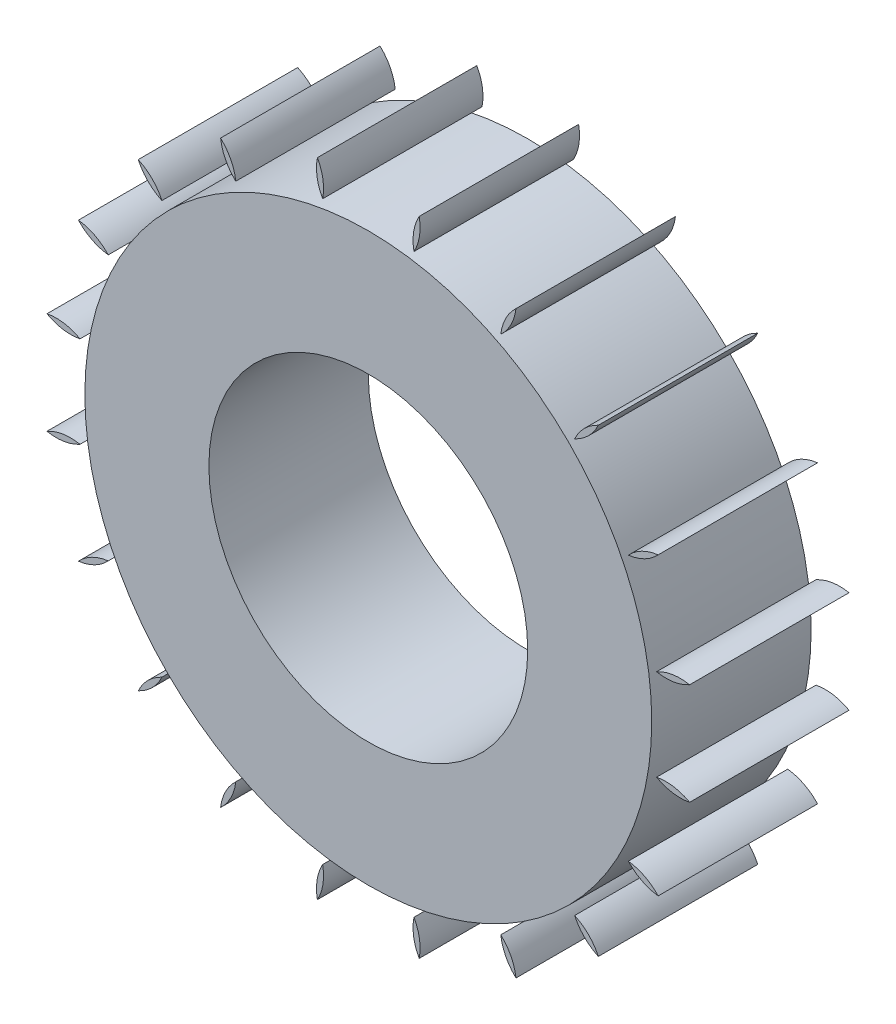
SolidWorks part; units mm, degrees
ref_plane "Front Plane" through (0, 0, 0) normal (0, 0, 1) x (1, 0, 0)
ref_plane "Top Plane" through (0, 0, 0) normal (0, 1, 0) x (1, 0, 0)
ref_plane "Right Plane" through (0, 0, 0) normal (1, 0, 0) x (0, 0, -1)
sketch "Sketch1" plane through (0, 0, 0) normal (0, 0, 1) x (1, 0, 0)
  circle A0 centre (0, 0) radius 6
  circle A1 centre (0, 0) radius 13.2
extrude "Boss-Extrude1" add sketch "Sketch1" along normal blind 6
sketch "Sketch2" plane through (0, 0, 6) normal (0, 0, 1) x (1, 0, 0)
  line L0 (0, 0) -> (0, 15.2) construction
  line L1 (-1.8199, 15.2) -> (0, 0) construction
  line L2 (1.8199, 15.2) -> (0, 0) construction
  arc A0 (-1.8199, 12) -> (1.8199, 12) centre (0, 0) cw
  arc A1 (-2.8199, 12.8953) -> (2.8199, 12.8953) centre (0, 0) cw
  arc A2 (-1.8199, 10.512) -> (1.8199, 10.512) centre (0, 0) cw
  arc A3 (-2.8199, 12.8953) -> (-1.8199, 10.512) centre (-3.5115, 11.2036) cw
  arc A4 (2.8199, 12.8953) -> (1.8199, 10.512) centre (3.5115, 11.2036) ccw
extrude "Cut-Extrude1" cut sketch "Sketch2" against normal through all contours A1 A4 A2 A3
pattern_circular "CirPattern3" count 20 over 360 about axis through (0, 0, 0) along (0, 0, 1) of "Cut-Extrude1"
